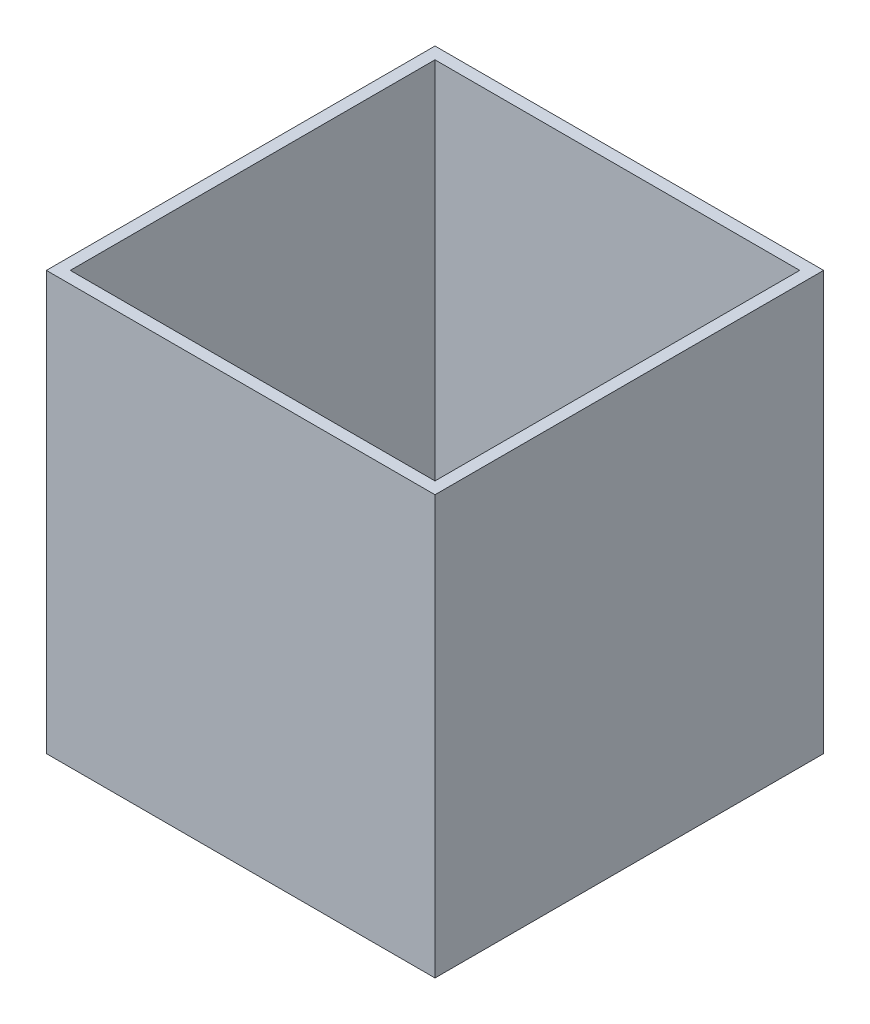
SolidWorks part; units mm, degrees
material "ABS"
ref_plane "Front Plane" through (0, 0, 0) normal (0, 0, 1) x (1, 0, 0)
ref_plane "Top Plane" through (0, 0, 0) normal (0, 1, 0) x (1, 0, 0)
ref_plane "Right Plane" through (0, 0, 0) normal (1, 0, 0) x (0, 0, -1)
sketch "Sketch1" plane through (0, 0, 0) normal (0, 1, 0) x (1, 0, 0)
  line L1 (0, 0) -> (82.55, 0)
  line L2 (0, 0) -> (0, -82.55)
  line L3 (0, -82.55) -> (82.55, -82.55)
  line L4 (82.55, 0) -> (82.55, -82.55)
extrude "Boss-Extrude1" add sketch "Sketch1" along normal blind 88.9
shell "Shell1" thickness 2.54
